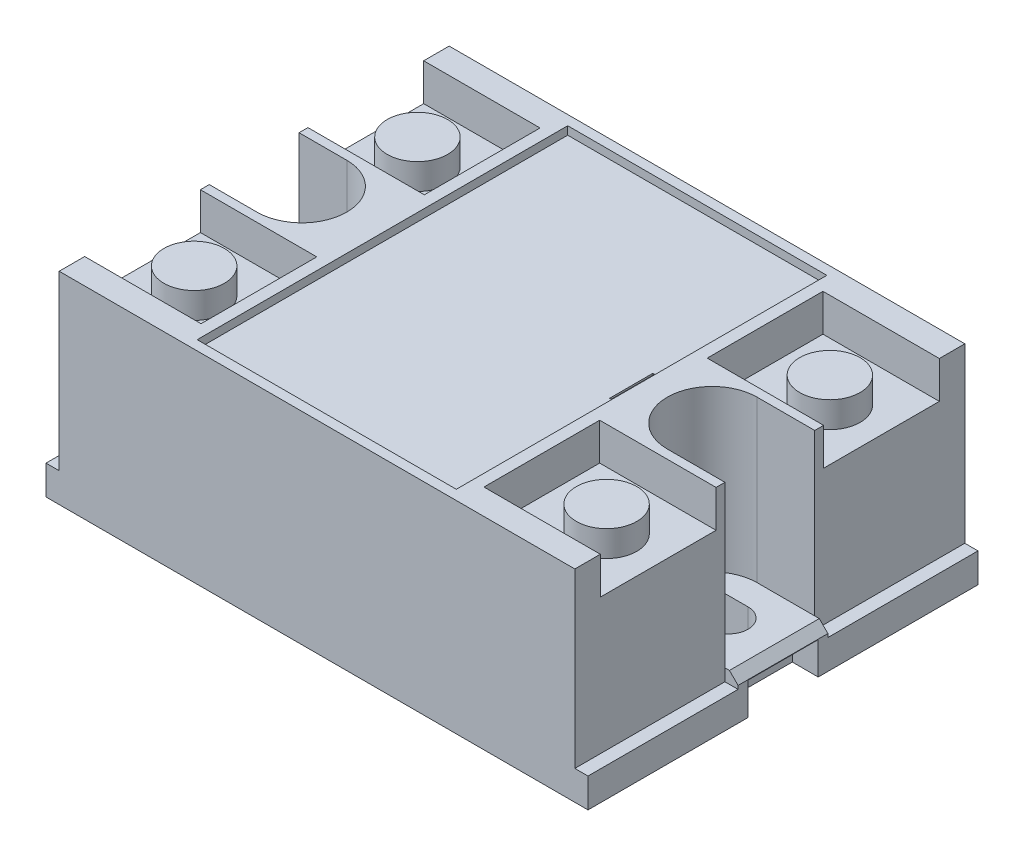
SolidWorks part; units mm, degrees
ref_plane "Front Plane" through (0, 0, 0) normal (0, 0, 1) x (1, 0, 0)
ref_plane "Top Plane" through (0, 0, 0) normal (0, 1, 0) x (1, 0, 0)
ref_plane "Right Plane" through (0, 0, 0) normal (1, 0, 0) x (0, 0, -1)
sketch "Sketch1" plane through (0, 0, 0) normal (0, 1, 0) x (1, 0, 0)
  line L1 (-31.375, -22.575) -> (31.375, -22.575)
  line L2 (-31.375, -22.575) -> (-31.375, 22.575)
  line L3 (-31.375, 22.575) -> (31.375, 22.575)
  line L4 (31.375, -22.575) -> (31.375, 22.575)
  line L5 (-31.375, -22.575) -> (31.375, 22.575) construction
  line L6 (-31.375, 22.575) -> (31.375, -22.575) construction
  point P0 (0, 0)
  dimension "D1" = 62.75
  dimension "D2" = 45.15
extrude "Boss-Extrude1" add sketch "Sketch1" along normal blind 23.4
sketch "Sketch2" plane through (0, 23.4, 0) normal (0, 1, 0) x (1, 0, 0)
  line L1 (-15, -21.45) -> (15, -21.45)
  line L2 (-15, -21.45) -> (-15, 21.45)
  line L3 (-15, 21.45) -> (15, 21.45)
  line L4 (15, -21.45) -> (15, 21.45)
  line L5 (-15, -21.45) -> (15, 21.45) construction
  line L6 (-15, 21.45) -> (15, -21.45) construction
  point P0 (0, 0)
  dimension "D1" = 30
  dimension "D2" = 42.9
extrude "Cut-Extrude1" cut sketch "Sketch2" against normal blind 0.95
sketch "Sketch3" plane through (0, 23.4, 0) normal (0, 1, 0) x (1, 0, 0)
  line L0 (-31.375, 22.575) -> (-31.375, -22.575) construction
  line L1 (-31.375, 19.625) -> (-16.375, 19.625)
  line L2 (-31.375, 19.625) -> (-31.375, 6.225)
  line L3 (-31.375, 6.225) -> (-16.375, 6.225)
  line L4 (-16.375, 19.625) -> (-16.375, 6.225)
  line L5 (-31.375, 0) -> (31.375, 0) construction
  line L6 (31.375, -22.575) -> (31.375, 22.575) construction
  line L7 (0, 22.575) -> (0, -22.575) construction
  line L8 (31.375, 22.575) -> (-31.375, 22.575) construction
  line L9 (-31.375, -22.575) -> (31.375, -22.575) construction
  line L10 (-16.375, -19.625) -> (-16.375, -6.225)
  line L11 (-31.375, -6.225) -> (-16.375, -6.225)
  line L12 (-31.375, -19.625) -> (-31.375, -6.225)
  line L13 (-31.375, -19.625) -> (-16.375, -19.625)
  line L14 (31.375, -19.625) -> (16.375, -19.625)
  line L15 (31.375, -19.625) -> (31.375, -6.225)
  line L16 (31.375, -6.225) -> (16.375, -6.225)
  line L17 (16.375, -19.625) -> (16.375, -6.225)
  line L18 (16.375, 19.625) -> (16.375, 6.225)
  line L19 (31.375, 6.225) -> (16.375, 6.225)
  line L20 (31.375, 19.625) -> (31.375, 6.225)
  line L21 (31.375, 19.625) -> (16.375, 19.625)
  dimension "D1" = 13.4
  dimension "D2" = 2.95
  dimension "D3" = 15
extrude "Cut-Extrude2" cut sketch "Sketch3" against normal blind 4.3
sketch "Sketch4" plane through (0, 19.1, 0) normal (0, 1, 0) x (1, 0, 0)
  line L0 (-23.875, 19.625) -> (-23.875, 6.225) construction
  line L1 (-16.375, 19.625) -> (-31.375, 19.625) construction
  line L2 (-31.375, 6.225) -> (-16.375, 6.225) construction
  line L3 (0, 22.575) -> (0, -22.575) construction
  line L4 (31.375, 22.575) -> (-31.375, 22.575) construction
  line L5 (-31.375, -22.575) -> (31.375, -22.575) construction
  line L6 (-31.375, 0) -> (31.375, 0) construction
  line L7 (-31.375, 6.225) -> (-31.375, -6.225) construction
  line L8 (31.375, -6.225) -> (31.375, 6.225) construction
  line L9 (-23.875, -19.625) -> (-23.875, -6.225) construction
  line L10 (23.875, -19.625) -> (23.875, -6.225) construction
  line L11 (23.875, 19.625) -> (23.875, 6.225) construction
  circle A0 centre (-23.875, 12.925) radius 3.5
  circle A1 centre (-23.875, -12.925) radius 3.5
  circle A2 centre (23.875, -12.925) radius 3.5
  circle A3 centre (23.875, 12.925) radius 3.5
  dimension "D1" = 7
extrude "Boss-Extrude2" add sketch "Sketch4" along normal blind 3
sketch "Sketch5" plane through (0, 23.4, 0) normal (0, 1, 0) x (1, 0, 0)
  line L0 (-31.375, 0) -> (-24.325, 0) construction
  line L3 (31.375, 0) -> (23.175, 0) construction
  line L4 (31.375, -6.225) -> (31.375, 6.225) construction
  line L5 (31.375, -5.2) -> (23.175, -5.2)
  line L6 (31.375, 5.2) -> (23.175, 5.2)
  line L7 (-31.375, 6.225) -> (-31.375, -6.225) construction
  line L8 (-31.375, 5.2) -> (-24.325, 5.2)
  line L9 (-31.375, -5.2) -> (-24.325, -5.2)
  arc A0 (31.375, -5.2) -> (31.375, 5.2) centre (31.375, 0) ccw
  arc A1 (23.175, 5.2) -> (23.175, -5.2) centre (23.175, 0) ccw
  arc A2 (-31.375, 5.2) -> (-31.375, -5.2) centre (-31.375, 0) ccw
  arc A3 (-24.325, -5.2) -> (-24.325, 5.2) centre (-24.325, 0) ccw
  point P4 (-27.85, 0)
  point P11 (27.275, 0)
  dimension "D1" = 10.4
  dimension "D2" = 13.4
  dimension "D3" = 12.25
extrude "Cut-Extrude3" cut sketch "Sketch5" against normal blind 18.6
sketch "Sketch6" plane through (0, 22.45, 0) normal (0, 1, 0) x (1, 0, 0)
  line L0 (31.375, 0) -> (0, 0) construction
  line L1 (31.375, -5.2) -> (31.375, 5.2) construction
  line L2 (14, 2.5) -> (14, -2.5)
  line L3 (15, -21.45) -> (15, 21.45) construction
  dimension "D1" = 1
  dimension "D2" = 5
extrude "Cut-Extrude-Thin1" cut sketch "Sketch6" against normal blind 1 and the other way through all thin
sketch "Sketch7" plane through (0, 4.8, 0) normal (0, 1, 0) x (1, 0, 0)
  line L0 (22.275, 0) -> (25.075, 0) construction
  line L1 (22.275, 2.25) -> (25.075, 2.25)
  line L2 (22.275, -2.25) -> (25.075, -2.25)
  line L3 (31.375, -5.2) -> (31.375, 5.2) construction
  arc A0 (22.275, 2.25) -> (22.275, -2.25) centre (22.275, 0) ccw
  arc A1 (25.075, -2.25) -> (25.075, 2.25) centre (25.075, 0) ccw
  point P3 (23.675, 0)
  dimension "D3" = 7.3
  dimension "D1" = 4.05
  dimension "D2" = 4.5
extrude "Cut-Extrude4" cut sketch "Sketch7" against normal through all
sketch "Sketch8" plane through (0, 4.8, 0) normal (0, 1, 0) x (1, 0, 0)
  line L0 (22.275, 0) -> (-31.375, 0) construction
  line L1 (-31.375, 5.2) -> (-31.375, -5.2) construction
  circle A0 centre (-23.825, 0) radius 2.25
  arc A3 (-24.325, -5.2) -> (-24.325, 5.2) centre (-24.325, 0) ccw construction
  dimension "D1" = 4.5
  dimension "D2" = 5.7
extrude "Cut-Extrude5" cut sketch "Sketch8" against normal through all
sketch "Sketch9" plane through (0, 23.4, 0) normal (0, 1, 0) x (1, 0, 0)
  line L0 (-31.375, -22.575) -> (31.375, -22.575) construction
  line L1 (-31.375, 22.575) -> (-29.85, 22.575)
  line L2 (-31.375, 22.575) -> (-31.375, -22.575)
  line L3 (-31.375, -22.575) -> (-29.85, -22.575)
  line L4 (-29.85, 22.575) -> (-29.85, -22.575)
  line L5 (0, 22.575) -> (0, -22.575) construction
  line L6 (31.375, 22.575) -> (-31.375, 22.575) construction
  line L7 (29.85, 22.575) -> (29.85, -22.575)
  line L8 (31.375, -22.575) -> (29.85, -22.575)
  line L9 (31.375, 22.575) -> (31.375, -22.575)
  line L10 (31.375, 22.575) -> (29.85, 22.575)
  dimension "D1" = 59.7
extrude "Cut-Extrude6" cut sketch "Sketch9" against normal blind 20
sketch "Sketch11" plane through (0, 3.4, 0) normal (0, 1, 0) x (1, 0, 0)
  line L0 (-31.375, 22.575) -> (-31.375, -22.575) construction
  line L1 (-29.85, 5.2) -> (-31.375, 5.2)
  line L2 (-29.85, 5.2) -> (-29.85, -5.2)
  line L3 (-29.85, -5.2) -> (-31.375, -5.2)
  line L4 (-31.375, 5.2) -> (-31.375, -5.2)
  line L5 (31.375, -22.575) -> (31.375, 22.575) construction
  line L6 (29.85, 5.2) -> (31.375, 5.2)
  line L7 (29.85, 5.2) -> (29.85, -5.2)
  line L8 (29.85, -5.2) -> (31.375, -5.2)
  line L9 (31.375, 5.2) -> (31.375, -5.2)
  line L10 (29.85, 22.575) -> (29.85, -22.575) construction
extrude "Boss-Extrude3" add sketch "Sketch11" along normal up to surface (1.4 mm away) up to face at (-25.7875, 4.8, 0)
chamfer "Chamfer1" distance 1 angle 45 2 edges at (31.375, 4.8, 0) (-31.375, 4.8, 0)
sketch "Sketch10" plane through (0, 0, 0) normal (0, -1, 0) x (1, 0, 0)
  line L0 (0, 22.575) -> (0, -22.575) construction
  line L1 (-31.375, 22.575) -> (31.375, 22.575) construction
  line L2 (31.375, -22.575) -> (-31.375, -22.575) construction
  line L3 (-31.375, 0) -> (31.375, 0) construction
  line L4 (-31.375, -22.575) -> (-31.375, 22.575) construction
  line L5 (31.375, 22.575) -> (31.375, -22.575) construction
  line L6 (-28.375, 4.075) -> (-31.375, -4.075) construction
  line L7 (28.375, -4.075) -> (31.375, -4.075)
  line L8 (28.375, -4.075) -> (28.375, 4.075)
  line L9 (28.375, 4.075) -> (31.375, 4.075)
  line L10 (31.375, -4.075) -> (31.375, 4.075)
  line L11 (28.375, -4.075) -> (31.375, 4.075) construction
  line L12 (28.375, 4.075) -> (31.375, -4.075) construction
  line L13 (-28.375, -4.075) -> (-31.375, 4.075) construction
  line L14 (-31.375, -4.075) -> (-31.375, 4.075)
  line L15 (-28.375, 4.075) -> (-31.375, 4.075)
  line L16 (-28.375, -4.075) -> (-28.375, 4.075)
  line L17 (-28.375, -4.075) -> (-31.375, -4.075)
  point P12 (29.875, 0)
  point P21 (-29.875, 0)
  dimension "D1" = 8.15
  dimension "D2" = 3
extrude "Cut-Extrude7" cut sketch "Sketch10" against normal blind 3.75
sketch "Sketch13"
